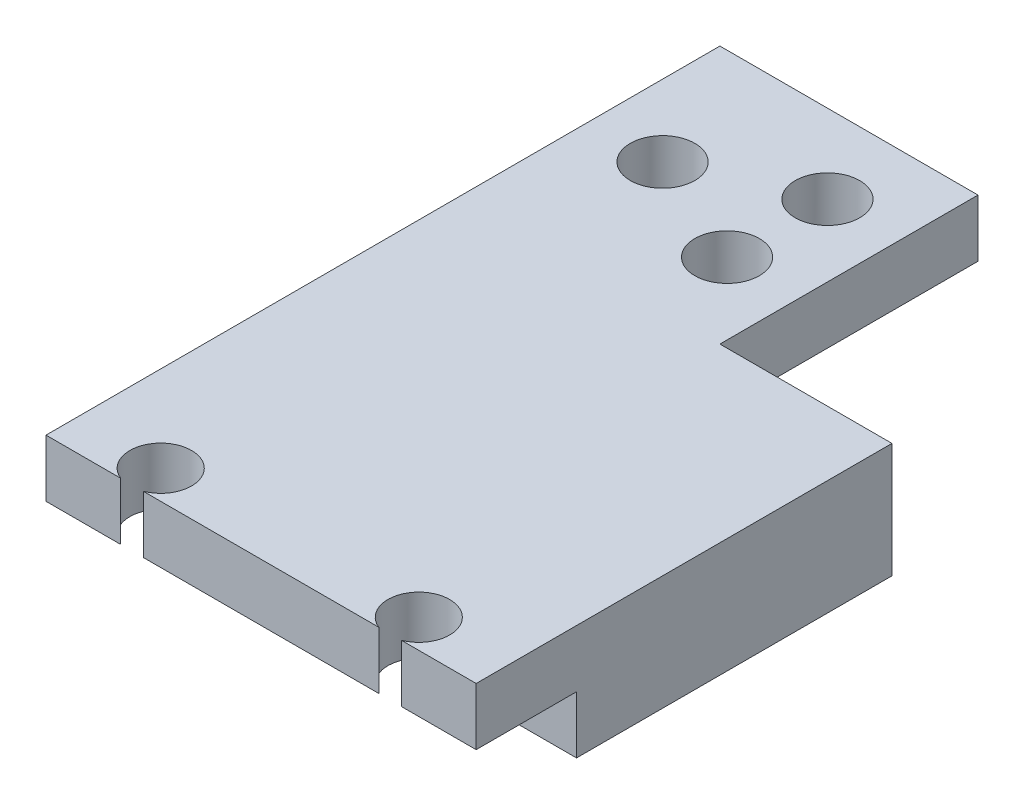
SolidWorks part; units mm, degrees
ref_plane "Front Plane" through (0, 0, 0) normal (0, 0, 1) x (1, 0, 0)
ref_plane "Top Plane" through (0, 0, 0) normal (0, 1, 0) x (1, 0, 0)
ref_plane "Right Plane" through (0, 0, 0) normal (1, 0, 0) x (0, 0, -1)
sketch "Sketch1" plane through (0, 0, 0) normal (0, 1, 0) x (1, 0, 0)
  line L0 (0, 0) -> (0, -14.5) construction
  line L1 (-15, -14.5) -> (-9.789, -14.5)
  line L2 (-15, -14.5) -> (-15, 14.5)
  line L3 (-15, 14.5) -> (15, 14.5)
  line L4 (15, -14.5) -> (15, 14.5)
  line L5 (-15, -14.5) -> (15, 14.5) construction
  line L6 (-15, 14.5) -> (15, -14.5) construction
  line L7 (-8.211, -14.5) -> (8.211, -14.5)
  line L8 (9.789, -14.5) -> (15, -14.5)
  arc A0 (-8.211, -14.5) -> (-9.789, -14.5) centre (-9, -12.5) ccw
  arc A2 (8.211, -14.5) -> (9.789, -14.5) centre (9, -12.5) cw
  point P0 (0, 0)
  dimension "D1" = 9
  dimension "D2" = 2
  dimension "D3" = 4.3
  dimension "D6" = 14.5
  dimension "D5" = 6
  dimension "D4" = 27
extrude "Boss-Extrude1" add sketch "Sketch1" along normal blind 4
sketch "Sketch2" plane through (0, 0, 0) normal (0, -1, 0) x (1, 0, 0)
  line L0 (-15, -14.5) -> (-15, 14.5) construction
  line L1 (15, -14.5) -> (-15, -14.5)
  line L2 (15, -14.5) -> (15, 7.5)
  line L3 (15, 7.5) -> (-15, 7.5)
  line L4 (-15, -14.5) -> (-15, 7.5)
  arc A0 (-9.789, 14.5) -> (-8.211, 14.5) centre (-9, 12.5) ccw construction
  dimension "D1" = 5
extrude "Boss-Extrude2" add sketch "Sketch2" along normal blind 4
sketch "Sketch3" plane through (0, 0, -14.5) normal (0, 0, -1) x (-1, 0, 0)
  line L0 (15, 4) -> (15, -4) construction
  line L5 (-15, 4) -> (-15, -4) construction
  line L6 (15, 0) -> (-15, 0)
  line L7 (15, 0) -> (15, 4)
  line L8 (15, 4) -> (-15, 4)
  line L9 (-15, 0) -> (-15, 4)
  point P4 (15, 4)
  point P7 (0, 0)
  point P11 (15, 4)
  dimension "D1" = 4
extrude "Boss-Extrude3" add sketch "Sketch3" along normal blind 18
sketch "Sketch4" plane through (0, 0, 0) normal (0, 1, 0) x (-1, 0, 0)
  line L0 (-15, -23.5) -> (15, -23.5) construction
  line L1 (-15, -32.5) -> (-15, -14.5) construction
  line L4 (15, -32.5) -> (15, 14.5) construction
  line L5 (15, -32.5) -> (15, -14.5) construction
  circle A0 centre (2, -27) radius 2.25
  circle A2 centre (10, -23.5) radius 2.25
  circle A4 centre (2, -20) radius 2.25
  dimension "D2" = 8
  dimension "D3" = 4.5
  dimension "D4" = 5
  dimension "D5" = 4.5
  dimension "D1" = 3.5
extrude "Cut-Extrude1" cut sketch "Sketch4" along normal up to next
sketch "Sketch5" plane through (0, 0, 0) normal (0, 1, 0) x (1, 0, 0)
  line L0 (-15, 32.5) -> (15, 32.5) construction
  line L1 (3, 32.5) -> (15, 32.5)
  line L2 (3, 32.5) -> (3, 14.5)
  line L3 (3, 14.5) -> (15, 14.5)
  line L4 (15, 32.5) -> (15, 14.5)
  line L5 (15, -14.5) -> (15, 32.5) construction
  line L6 (15, 32.5) -> (15, 14.5) construction
  line L7 (15, 14.5) -> (-15, 14.5) construction
  circle A0 centre (-2, 27) radius 2.25 construction
  point P9 (0, 0)
  point P10 (15, 14.3998)
  point P13 (15, 14.5)
  point P16 (3, 14.5)
  dimension "D1" = 5
extrude "Cut-Extrude2" cut sketch "Sketch5" along normal up to next
